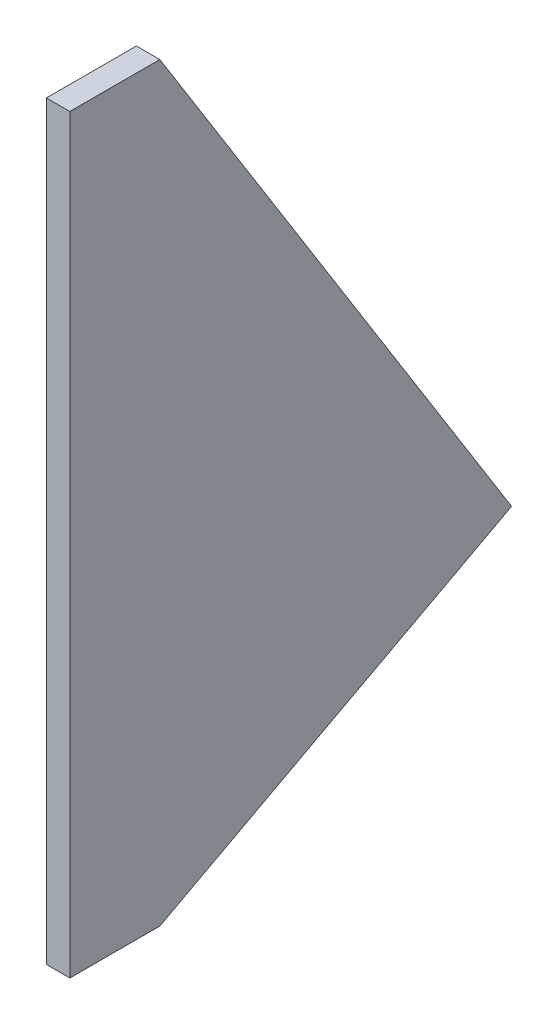
SolidWorks part; units mm, degrees
material "Thornel Mat VMA"
ref_plane "Front Plane" through (0, 0, 0) normal (0, 0, 1) x (1, 0, 0)
ref_plane "Top Plane" through (0, 0, 0) normal (0, 1, 0) x (1, 0, 0)
ref_plane "Right Plane" through (0, 0, 0) normal (1, 0, 0) x (0, 0, -1)
sketch "Sketch1" plane through (0, 0, 0) normal (1, 0, 0) x (0, 0, -1)
  line L0 (0, 0) -> (0, 203.2)
  line L1 (0, 203.2) -> (24.3586, 203.2)
  line L2 (24.3586, 203.2) -> (119.6086, 50.8)
  line L3 (119.6086, 50.8) -> (24.3586, 0)
  line L4 (24.3586, 0) -> (0, 0)
  dimension "D1" = 203.2
  dimension "D2" = 152.4
  dimension "D3" = 95.25
  dimension "D4" = 24.3586
extrude "Boss-Extrude1" add sketch "Sketch1" along normal mid plane 6.35
